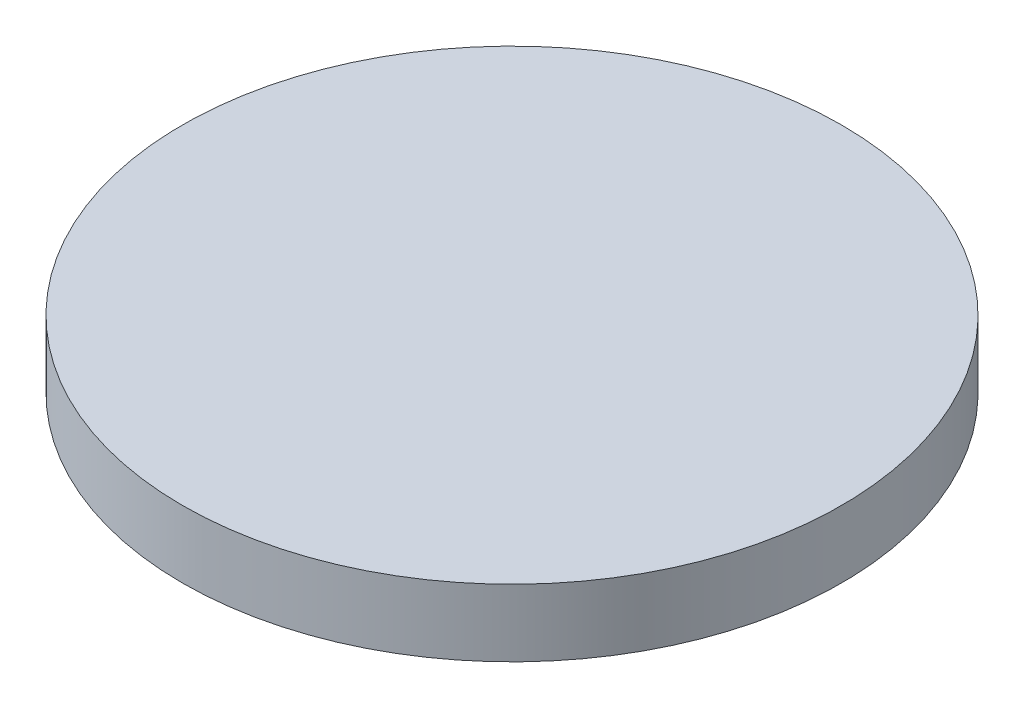
SolidWorks part; units mm, degrees
ref_plane "Front Plane" through (0, 0, 0) normal (0, 0, 1) x (1, 0, 0)
ref_plane "Top Plane" through (0, 0, 0) normal (0, 1, 0) x (1, 0, 0)
ref_plane "Right Plane" through (0, 0, 0) normal (1, 0, 0) x (0, 0, -1)
sketch "Sketch1" plane through (0, 0, 0) normal (0, 1, 0) x (1, 0, 0)
  circle A0 centre (0, 0) radius 9805
  dimension "D1" = 19610
extrude "Boss-Extrude1" add sketch "Sketch1" along normal mid plane 2000
